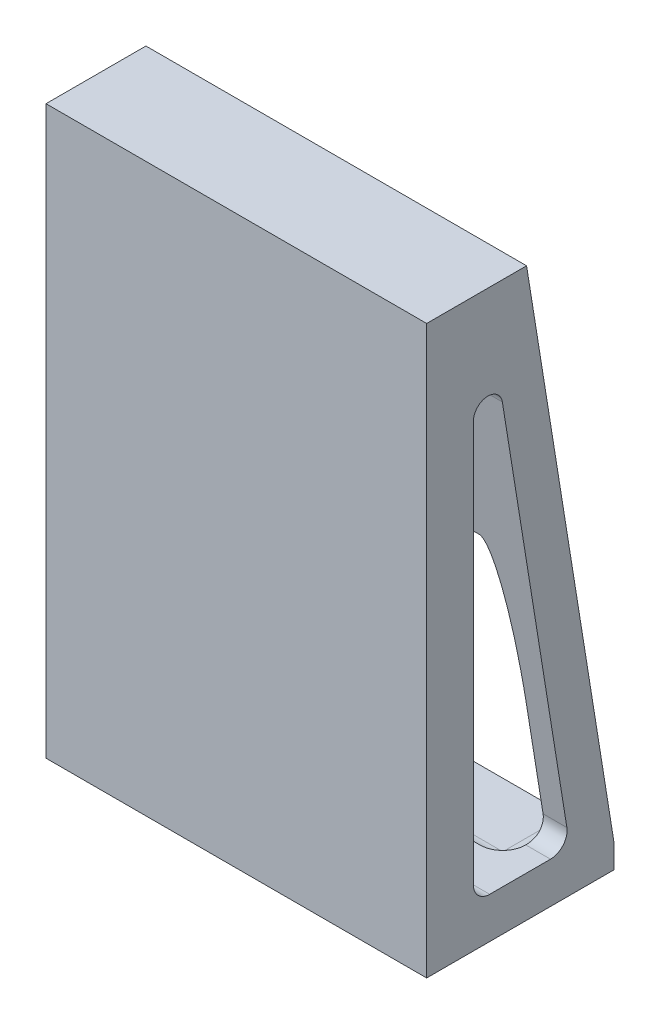
SolidWorks part; units mm, degrees
ref_plane "Front Plane" through (0, 0, 0) normal (0, 0, 1) x (1, 0, 0)
ref_plane "Top Plane" through (0, 0, 0) normal (0, 1, 0) x (1, 0, 0)
ref_plane "Right Plane" through (0, 0, 0) normal (1, 0, 0) x (0, 0, -1)
sketch "Sketch1" plane through (0, 0, 0) normal (0, 1, 0) x (1, 0, 0)
  line L0 (0, 0) -> (0, 40) construction
  line L1 (-76.2, 40) -> (76.2, 40)
  line L2 (-76.2, 40) -> (-76.2, 0)
  line L3 (-76.2, 0) -> (76.2, 0)
  line L4 (76.2, 40) -> (76.2, 0)
  dimension "D1" = 0
  dimension "D2" = 152.4
  dimension "D3" = 40
extrude "Boss-Extrude1" add sketch "Sketch1" along normal blind 179.05 and the other way blind 100
ref_plane "Plane1" through (0, -47.895, 0) normal (0, 1, 0) x (1, 0, 0)
ref_plane "Plane2" through (0, -47.895, 0) normal (0, 1, 0) x (1, 0, 0)
other "SurfaceCut1"
sketch "Sketch3" plane through (0, 0, 0) normal (1, 0, 0) x (0, 0, -1)
  line L0 (0, -47.895) -> (40, -47.895) construction
  line L1 (0, -38.37) -> (75, -38.37)
  line L2 (0, -38.37) -> (0, -47.895)
  line L3 (0, -47.895) -> (75, -47.895)
  line L4 (75, -38.37) -> (75, -47.895)
  dimension "D1" = 9.525
  dimension "D2" = 75
extrude "Boss-Extrude2" add sketch "Sketch3" along normal up to surface and the other way up to surface up to face at (76.2, 65.5775, -20) other way up to face at (-76.2, 65.5775, -20)
sketch "Sketch4" plane through (76.2, 0, 0) normal (1, 0, 0) x (0, 0, -1)
  line L0 (40, 179.05) -> (75, -38.37)
rib "Rib1" sketch "Sketch4" sketch "Sketch4" thickness 9.525 extrusion direction parallel to sketch draft on no parameters "D1"=9.525
mirror "Mirror1" about plane through (0, 0, 0) normal (1, 0, 0) of "Rib1"
sketch "Sketch5" [suppressed] plane through (0, 0, 0) normal (0, 1, 0) x (1, 0, 0)
  line L12 (-47.625, 55.95) -> (-47.625, 49.05)
  line L13 (-47.625, 49.05) -> (47.625, 49.05)
  line L14 (47.625, 49.05) -> (47.625, 55.95)
  line L15 (47.625, 55.95) -> (-47.625, 55.95)
  line L16 (-47.625, 55.95) -> (-47.625, 49.05) construction
  line L17 (-47.625, 49.05) -> (47.625, 49.05) construction
  line L18 (47.625, 49.05) -> (47.625, 55.95) construction
  line L19 (47.625, 55.95) -> (-47.625, 55.95) construction
  dimension "D1" = 19.05
fillet "Fillet1" radius 9.525 5 edges at (-66.675, -38.37, -57.5) (-66.675, 70.34, -40) (0, -38.37, -40) (66.675, -38.37, -57.5) (66.675, 70.34, -40)
hole_wizard "3/8 Clearance Hole1" [suppressed] positions "Sketch6" profile "Sketch7" hole size "3/8" standard "ANSI Inch"
sketch "Sketch6" [suppressed] plane through (0, -38.37, 0) normal (0, 1, 0) x (1, 0, 0)
  line L0 (47.625, 55.95) -> (-47.625, 55.95) construction
  point P0 (47.625, 55.95)
  point P4 (-47.625, 55.95)
  point P6 (0, 55.95)
sketch "Sketch7" plane through (47.625, -38.37, -55.95) normal (1, 0, 0) x (0, 0, 1)
  line L0 (0, 0) -> (0, 9.525)
  line L1 (0, 9.525) -> (5.1587, 9.525)
  line L2 (5.1587, 9.525) -> (5.1587, 0)
  line L5 (5.1587, 0) -> (0, 0)
  line L11 (0, -6.35) -> (0, 107.95) construction
  dimension "Thru Hole Dia." = 10.3175
  dimension "Thru Hole Depth" = 9.525
sketch "Sketch8" plane through (0, 0, 0) normal (1, 0, 0) x (0, 0, -1)
  line L0 (40, 179.05) -> (75, -38.37) construction
  line L6 (22.9621, 159.05) -> (20, 159.05)
  line L7 (22.9621, 159.05) -> (20, 159.05)
  line L10 (20, -27.895) -> (53.0563, -27.895)
  line L11 (53.0563, -27.895) -> (22.9621, 159.05)
  line L12 (20, 159.05) -> (20, -27.895)
  line L13 (25.2367, -31.4875) -> (49.5762, -31.4875)
  line L14 (56.1356, -23.7877) -> (30.3013, 136.6949)
  line L15 (18.6975, 135.7669) -> (18.6975, -24.9483)
  arc A0 (49.5762, -31.4875) -> (56.1356, -23.7877) centre (49.5762, -24.8437) ccw
  arc A3 (18.6975, -24.9483) -> (25.2367, -31.4875) centre (25.2367, -24.9483) ccw
  arc A4 (18.6975, 135.7669) -> (30.3013, 136.6949) centre (24.5365, 135.7669) cw
  dimension "D1" = 20
extrude "Cut-Extrude1" cut sketch "Sketch8" against normal up to surface and the other way up to surface contours L14 A4 L15 A3 L13 A0 up to face at (-76.2, 44.788, -38) other way up to face at (76.2, 44.788, -38)
